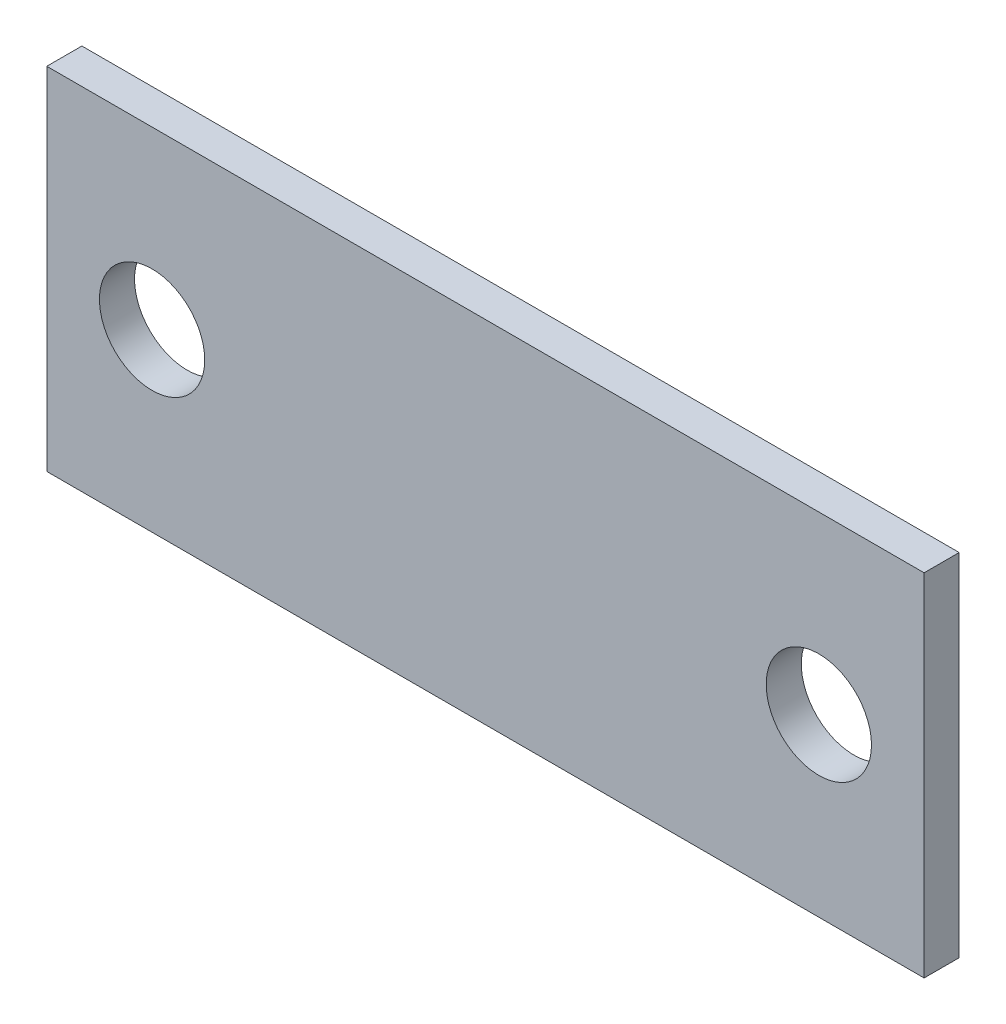
SolidWorks part; units mm, degrees
ref_plane "Спереди" through (0, 0, 0) normal (0, 0, 1) x (1, 0, 0)
ref_plane "Сверху" through (0, 0, 0) normal (0, 1, 0) x (1, 0, 0)
ref_plane "Справа" through (0, 0, 0) normal (1, 0, 0) x (0, 0, -1)
other "Configuration Table"
sketch "Эскиз1" plane through (0, 0, 0) normal (0, 0, 1) x (1, 0, 0)
  line L0 (-95, 0) -> (95, 0) construction
  line L1 (-125, -50) -> (125, -50)
  line L2 (-125, -50) -> (-125, 50)
  line L3 (-125, 50) -> (125, 50)
  line L4 (125, -50) -> (125, 50)
  line L5 (-125, -50) -> (125, 50) construction
  line L6 (-125, 50) -> (125, -50) construction
  circle A0 centre (-95, 0) radius 15
  circle A1 centre (95, 0) radius 15
  point P0 (0, 0)
  point P10 (0, 0)
  dimension "D3" = 30
  dimension "D4" = 30
  dimension "D1" = 250
  dimension "D2" = 100
extrude "Бобышка-Вытянуть1" add sketch "Эскиз1" along normal blind 10
